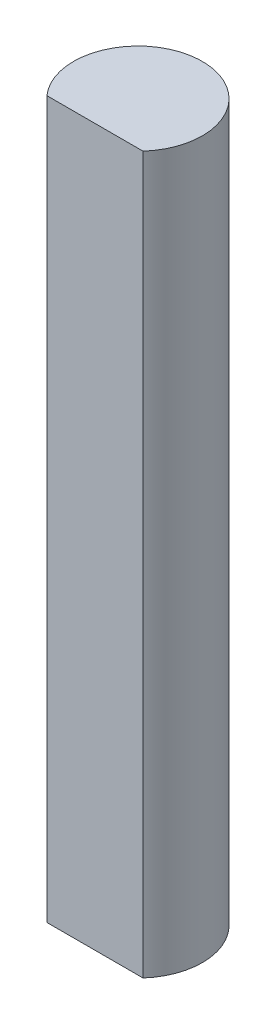
SolidWorks part; units mm, degrees
ref_plane "Front Plane" through (0, 0, 0) normal (0, 0, 1) x (1, 0, 0)
ref_plane "Top Plane" through (0, 0, 0) normal (0, 1, 0) x (1, 0, 0)
ref_plane "Right Plane" through (0, 0, 0) normal (1, 0, 0) x (0, 0, -1)
sketch "Sketch2" plane through (0, 0, 0) normal (0, 1, 0) x (1, 0, 0)
  circle A0 centre (0, 0) radius 2.25
extrude "Boss-Extrude1" add sketch "Sketch2" along normal blind 25
sketch "Sketch4" plane through (0, 25, 0) normal (0, 1, 0) x (1, 0, 0)
  line L0 (0, -2.25) -> (0, -1.5) construction
  line L1 (-2.3126, -1.5) -> (2.3126, -1.5)
  line L2 (2.3126, -1.5) -> (2.3126, -2.3962)
  line L3 (2.3126, -2.3962) -> (-2.3126, -2.3962)
  line L4 (-2.3126, -2.3962) -> (-2.3126, -1.5)
  circle A0 centre (0, 0) radius 2.25 construction
  point P9 (0, -1.5)
extrude "Cut-Extrude1" cut sketch "Sketch4" against normal blind 25
